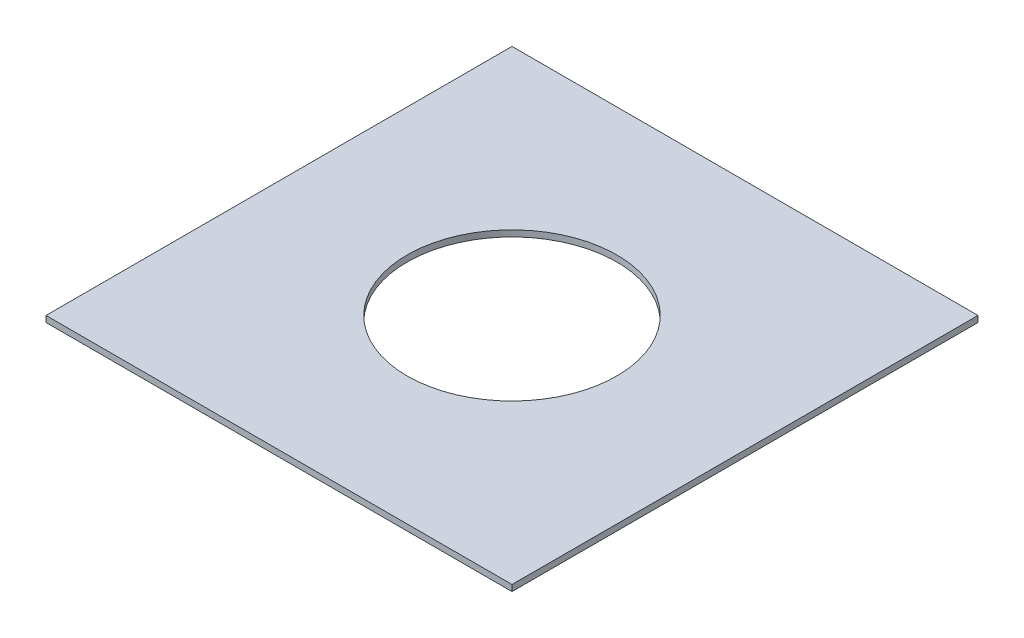
SolidWorks part; units mm, degrees
material "PTFE (general)"
ref_plane "Front Plane" through (0, 0, 0) normal (0, 0, 1) x (1, 0, 0)
ref_plane "Top Plane" through (0, 0, 0) normal (0, 1, 0) x (1, 0, 0)
ref_plane "Right Plane" through (0, 0, 0) normal (1, 0, 0) x (0, 0, -1)
sketch "Sketch1" plane through (0, 0, 0) normal (0, 1, 0) x (1, 0, 0)
  line L12 (17.5573, 30.5402) -> (17.5573, -29.4598)
  line L13 (17.5573, -29.4598) -> (77.5573, -29.4598)
  line L14 (77.5573, -29.4598) -> (77.5573, 30.5402)
  line L16 (17.5573, 30.5402) -> (77.5573, 30.5402)
  circle A2 centre (47.5573, 0.5402) radius 13.5
  circle A3 centre (47.5573, 0.5402) radius 13.5
  dimension "D1" = 0
extrude "Boss-Extrude1" add sketch "Sketch1" along normal blind 0.7937
